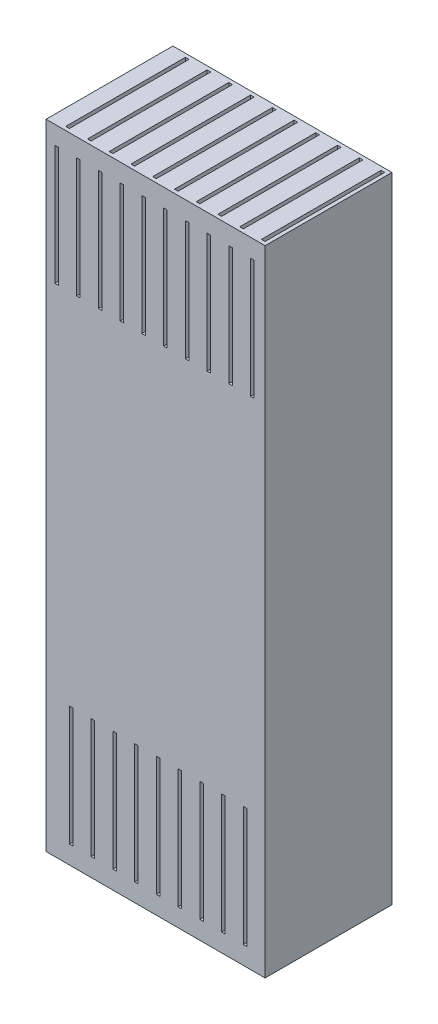
SolidWorks part; units mm, degrees
material "Nickel"
ref_plane "Front Plane" through (0, 0, 0) normal (0, 0, 1) x (1, 0, 0)
ref_plane "Top Plane" through (0, 0, 0) normal (0, 1, 0) x (1, 0, 0)
ref_plane "Right Plane" through (0, 0, 0) normal (1, 0, 0) x (0, 0, -1)
sketch "Sketch1" plane through (0, 0, 0) normal (0, 1, 0) x (1, 0, 0)
  line L1 (-60.4258, -35) -> (60.4258, -35)
  line L2 (-60.4258, -35) -> (-60.4258, 35)
  line L3 (-60.4258, 35) -> (60.4258, 35)
  line L4 (60.4258, -35) -> (60.4258, 35)
  line L5 (-60.4258, -35) -> (60.4258, 35) construction
  line L6 (-60.4258, 35) -> (60.4258, -35) construction
  point P0 (0, 0)
extrude "Boss-Extrude1" add sketch "Sketch1" along normal blind 350
sketch "Sketch2" plane through (0, 350, 0) normal (0, 1, 0) x (1, 0, 0)
  line L0 (60.4258, 35) -> (58.4258, 35) construction
  line L1 (60.4258, 35) -> (-60.4258, 35) construction
  line L2 (58.4258, 35) -> (58.4258, 33) construction
  line L3 (60.4258, -35) -> (60.4258, -33) construction
  line L4 (60.4258, -35) -> (60.4258, 35) construction
  line L5 (60.4258, -33) -> (58.4258, -33) construction
  line L7 (58.4258, -33) -> (56.4258, -33)
  line L8 (58.4258, -33) -> (58.4258, 33)
  line L9 (58.4258, 33) -> (56.4258, 33)
  line L10 (56.4258, -33) -> (56.4258, 33)
  point P14 (0, 0)
extrude "Cut-Extrude1" cut sketch "Sketch2" against normal blind 350
pattern_linear "LPattern1" count 10 spacing 12 along (-1, 0, 0) of "Cut-Extrude1"
sketch "Sketch3" plane through (0, 350, 0) normal (0, 1, 0) x (1, 0, 0)
  line L0 (56.4258, 33) -> (54.4258, 33) construction
  line L2 (54.4258, 33) -> (52.4258, 33)
  line L3 (54.4258, 33) -> (54.4258, -33)
  line L4 (54.4258, -33) -> (52.4258, -33)
  line L5 (52.4258, 33) -> (52.4258, -33)
  point P6 (0, 0)
  point P7 (0, 0)
extrude "Cut-Extrude2" cut sketch "Sketch3" against normal blind 340
pattern_linear "LPattern2" count 10 spacing 12 along (-1, 0, 0) of "Cut-Extrude2"
sketch "Sketch4" plane through (0, 0, 0) normal (0, -1, 0) x (1, 0, 0)
  line L0 (-49.5742, 33) -> (-47.5742, 33) construction
  line L2 (-47.5742, 33) -> (-45.5742, 33)
  line L3 (-47.5742, 33) -> (-47.5742, -33)
  line L4 (-47.5742, -33) -> (-45.5742, -33)
  line L5 (-45.5742, 33) -> (-45.5742, -33)
  point P6 (0, 0)
extrude "Cut-Extrude3" cut sketch "Sketch4" against normal blind 340
pattern_linear "LPattern3" count 10 spacing 12 along (1, 0, 0) of "Cut-Extrude3"
sketch "Sketch5" plane through (0, 0, -35) normal (0, 0, -1) x (-1, 0, 0)
  line L0 (-60.4258, 350) -> (-50.4258, 350) construction
  line L1 (-60.4258, 350) -> (60.4258, 350) construction
  line L2 (-50.4258, 350) -> (-50.4258, 340) construction
  line L4 (-50.4258, 340) -> (-48.4258, 340)
  line L5 (-50.4258, 340) -> (-50.4258, 274)
  line L6 (-50.4258, 274) -> (-48.4258, 274)
  line L7 (-48.4258, 340) -> (-48.4258, 274)
  point P9 (0, 0)
extrude "Cut-Extrude4" cut sketch "Sketch5" against normal blind 68
pattern_linear "LPattern4" count 9 spacing 12 along (-1, 0, 0) of "Cut-Extrude4"
sketch "Sketch6" plane through (0, 0, 35) normal (0, 0, 1) x (1, 0, 0)
  line L0 (60.4258, 0) -> (50.4258, 0) construction
  line L1 (50.4258, 0) -> (50.4258, 10) construction
  line L3 (50.4258, 10) -> (48.4258, 10)
  line L4 (50.4258, 10) -> (50.4258, 76)
  line L5 (50.4258, 76) -> (48.4258, 76)
  line L6 (48.4258, 10) -> (48.4258, 76)
  point P8 (0, 0)
extrude "Cut-Extrude5" cut sketch "Sketch6" against normal blind 68
pattern_linear "LPattern5" count 9 spacing 12 along (-1, 0, 0) of "Cut-Extrude5"
sketch "Sketch7" plane through (0, 0, -35) normal (0, 0, -1) x (-1, 0, 0)
  line L0 (-60.4258, 0) -> (-54.4258, 0) construction
  line L1 (-60.4258, 0) -> (60.4258, 0) construction
  line L2 (-54.4258, 0) -> (-54.4258, 10) construction
  line L4 (-54.4258, 10) -> (-52.4258, 10)
  line L5 (-54.4258, 10) -> (-54.4258, 76)
  line L6 (-54.4258, 76) -> (-52.4258, 76)
  line L7 (-52.4258, 10) -> (-52.4258, 76)
extrude "Cut-Extrude6" cut sketch "Sketch7" against normal blind 68
pattern_linear "LPattern6" count 10 spacing 12 along (-1, 0, 0) of "Cut-Extrude6"
sketch "Sketch8" plane through (0, 0, 35) normal (0, 0, 1) x (1, 0, 0)
  line L0 (60.4258, 350) -> (60.4258, 340) construction
  line L1 (60.4258, 350) -> (60.4258, 0) construction
  line L2 (60.4258, 340) -> (54.4258, 340) construction
  line L4 (54.4258, 340) -> (52.4258, 340)
  line L5 (54.4258, 340) -> (54.4258, 274)
  line L6 (54.4258, 274) -> (52.4258, 274)
  line L7 (52.4258, 340) -> (52.4258, 274)
  point P9 (0, 0)
extrude "Cut-Extrude7" cut sketch "Sketch8" against normal blind 68
pattern_linear "LPattern7" count 10 spacing 12 along (-1, 0, 0) of "Cut-Extrude7"
sketch "Sketch9" plane through (0, 350, 0) normal (0, 1, 0) x (1, 0, 0)
  line L0 (60.4258, 35) -> (54.4258, 35) construction
  line L1 (54.4258, 35) -> (54.4258, 33) construction
  line L3 (54.4258, 33) -> (52.4258, 33)
  line L4 (54.4258, 33) -> (54.4258, -33)
  line L5 (54.4258, -33) -> (52.4258, -33)
  line L6 (52.4258, 33) -> (52.4258, -33)
extrude "Boss-Extrude2" add sketch "Sketch9" against normal blind 10 separate body
ref_plane "Plane1" through (0, 10, 0) normal (0, -1, 0) x (-1, 0, 0)
ref_plane "Plane2" through (0, 340, 0) normal (0, 1, 0) x (1, 0, 0)
pattern_linear "LPattern9" count 10 spacing 12 along (-1, 0, 0) of "Boss-Extrude2"
combine bodies "Combine2" operation type add bodies to combine 115 127 128 129 130 131 132 133 134 135 116
sketch "Sketch11" plane through (0, 0, 0) normal (0, -1, 0) x (1, 0, 0)
  line L1 (50.4258, -33) -> (48.4258, -33)
  line L2 (50.4258, -33) -> (50.4258, 33)
  line L3 (50.4258, 33) -> (48.4258, 33)
  line L4 (48.4258, -33) -> (48.4258, 33)
extrude "Boss-Extrude4" add sketch "Sketch11" against normal blind 10
pattern_linear "LPattern10" count 9 spacing 12 along (-1, 0, 0) of "Boss-Extrude4"
